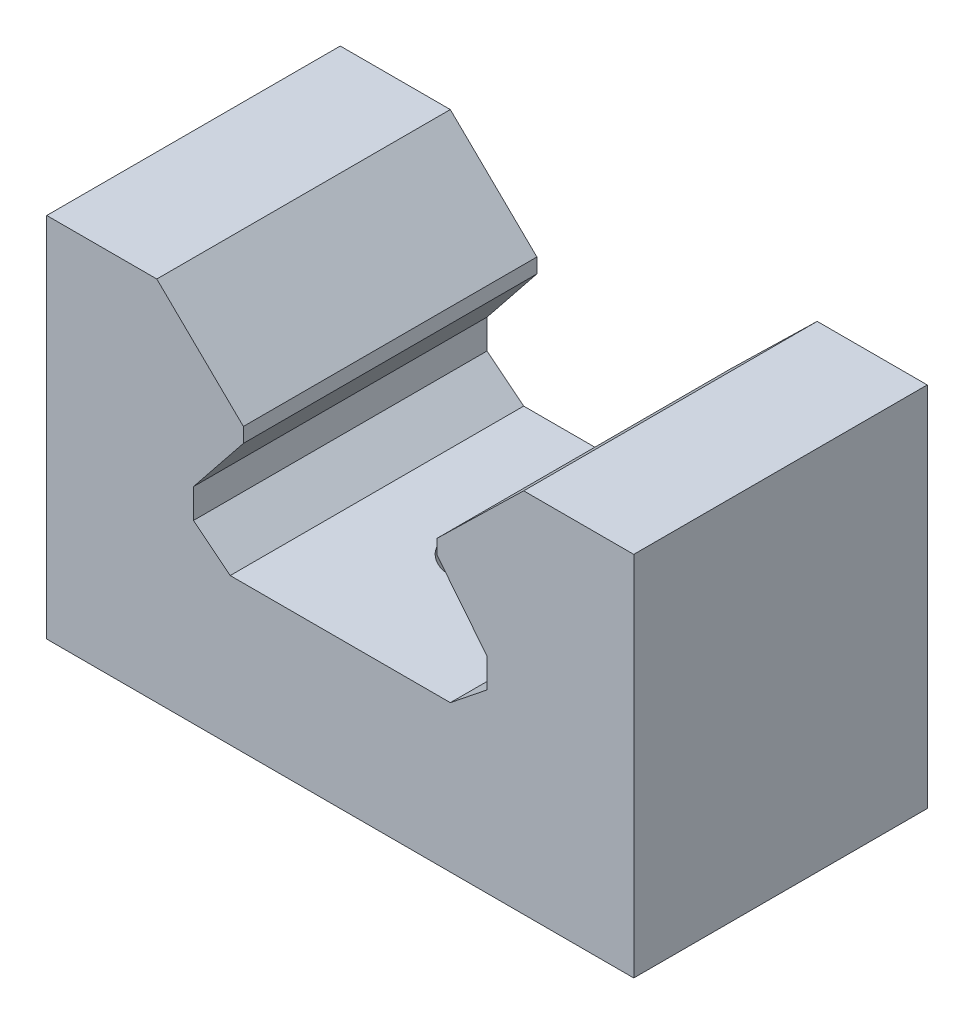
SolidWorks part; units mm, degrees
ref_plane "前视基准面" through (0, 0, 0) normal (0, 0, 1) x (1, 0, 0)
ref_plane "上视基准面" through (0, 0, 0) normal (0, 1, 0) x (1, 0, 0)
ref_plane "右视基准面" through (0, 0, 0) normal (1, 0, 0) x (0, 0, -1)
sketch "草图1" plane through (0, 0, 0) normal (0, 0, 1) x (1, 0, 0)
  line L1 (-20, 12.5) -> (20, 12.5)
  line L2 (-20, 12.5) -> (-20, -12.5)
  line L3 (-20, -12.5) -> (20, -12.5)
  line L4 (20, 12.5) -> (20, -12.5)
  line L5 (-20, 12.5) -> (20, -12.5) construction
  line L6 (-20, -12.5) -> (20, 12.5) construction
  point P0 (0, 0)
  dimension "D1" = 40
  dimension "D2" = 25
extrude "凸台-拉伸1" add sketch "草图1" along normal blind 20
sketch "草图2" plane through (0, 0, 0) normal (0, 0, -1) x (-1, 0, 0)
  line L0 (7.5, -2.5) -> (10, -0.5)
  line L1 (-20, 12.5) -> (20, 12.5) construction
  line L2 (-7.5, -2.5) -> (7.5, -2.5)
  line L3 (10, -0.5) -> (10, 1.5)
  line L4 (0, 0) -> (0, 20.7928) construction
  line L5 (-10, -0.5) -> (-10, 1.5)
  line L6 (-7.5, -2.5) -> (-10, -0.5)
  line L7 (10, 1.5) -> (6.6, 5.75)
  line L8 (6.6, 5.75) -> (6.6, 6.75)
  line L9 (6.6, 6.75) -> (12.5, 12.5)
  line L10 (-6.6, 6.75) -> (-12.5, 12.5)
  line L11 (-6.6, 5.75) -> (-6.6, 6.75)
  line L12 (-10, 1.5) -> (-6.6, 5.75)
  line L13 (-20, -12.5) -> (-20, 12.5) construction
  dimension "D1" = 15
  dimension "D2" = 15
  dimension "D3" = 20
  dimension "D4" = 20
  dimension "D5" = 2
  dimension "D6" = 13.2
  dimension "D7" = 25
  dimension "D8" = 1
  dimension "D9" = 2
extrude "切除-拉伸1" cut sketch "草图2" against normal blind 20 and the other way through all
ref_plane "基准面1" through (0, 0, 0) normal (1, 0, 0) x (0, 0, -1)
hole_wizard "M6 螺纹孔1" positions "草图3" profile "草图4" tap size "M6" standard "GB"
sketch "草图3" plane through (0, -12.5, 0) normal (0, -1, 0) x (-1, 0, 0)
  line L0 (0, 11) -> (0, -11) construction
  line L1 (20, -20) -> (-20, -20) construction
  point P0 (0, -10)
  dimension "D1" = 10
sketch "草图4" plane through (0, -12.5, 10) normal (1, 0, 0) x (0, 0, -1)
  line L0 (0, 0) -> (0, 19.5022)
  line L1 (0, 19.5022) -> (2.5, 18)
  line L2 (2.5, 18) -> (2.5, 0)
  line L5 (2.5, 0) -> (0, 0)
  line L10 (0, 19.5022) -> (-2.5, 18) construction
  line L11 (0, -6.35) -> (0, 107.95) construction
  dimension "螺纹孔钻头直径" = 5
  dimension "螺纹孔钻头深度" = 18
  dimension "导头角度" = 118
cosmetic thread "孔螺蚊线1" parameters "D1"=12, "D2"=6
